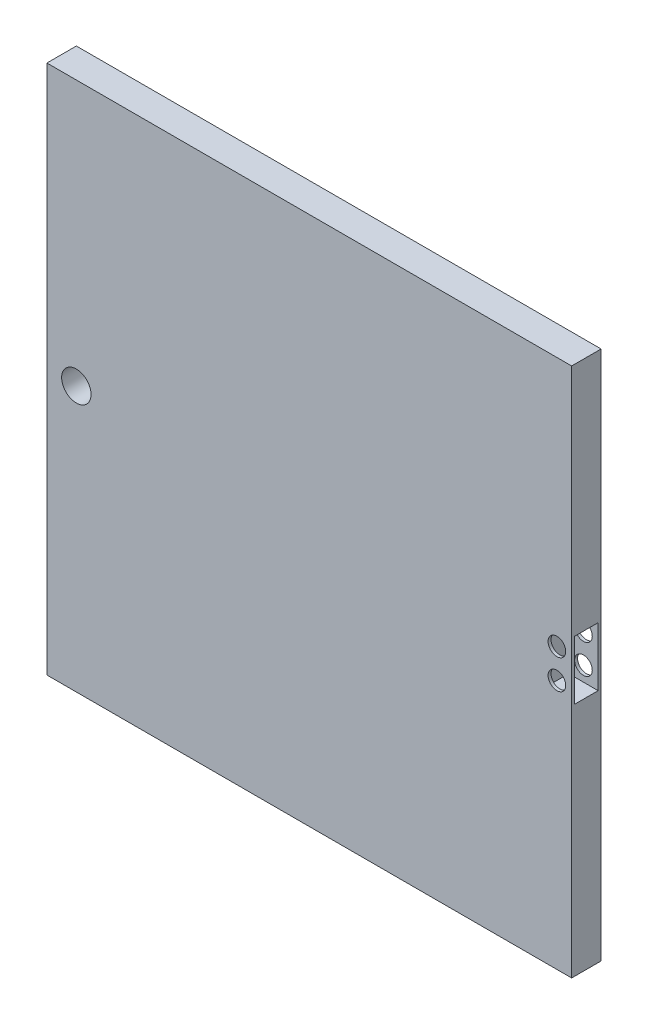
SolidWorks part; units mm, degrees
material "PET"
ref_plane "Front Plane" through (0, 0, 0) normal (0, 0, 1) x (1, 0, 0)
ref_plane "Top Plane" through (0, 0, 0) normal (0, 1, 0) x (1, 0, 0)
ref_plane "Right Plane" through (0, 0, 0) normal (1, 0, 0) x (0, 0, -1)
sketch "Sketch1" plane through (0, 0, 0) normal (0, 0, 1) x (1, 0, 0)
  line L1 (-78.2272, 89.1981) -> (148.0868, 89.1981)
  line L2 (-78.2272, 89.1981) -> (-78.2272, -126.7019)
  line L3 (-78.2272, -126.7019) -> (148.0868, -126.7019)
  line L4 (148.0868, 89.1981) -> (148.0868, -126.7019)
  dimension "D1" = 215.9
  dimension "D2" = 226.314
extrude "Boss-Extrude1" add sketch "Sketch1" along normal blind 12.7
sketch "Sketch2" plane through (148.0868, 0, 0) normal (1, 0, 0) x (0, 0, -1)
  line L1 (-11.43, 0.3061) -> (-1.27, 0.3061)
  line L2 (-11.43, 0.3061) -> (-11.43, -25.0939)
  line L3 (-11.43, -25.0939) -> (-1.27, -25.0939)
  line L4 (-1.27, 0.3061) -> (-1.27, -25.0939)
  line L6 (-12.7, -126.7019) -> (-12.7, 89.1981) construction
  point P6 (-6.35, 0.3061)
  point P8 (-1.27, -12.3939)
  dimension "D1" = 25.4
  dimension "D2" = 101.6
  dimension "D3" = 10.16
  dimension "D4" = 6.35
extrude "Cut-Extrude1" cut sketch "Sketch2" against normal blind 12.7
sketch "Sketch3" plane through (0, 0, 12.7) normal (0, 0, 1) x (1, 0, 0)
  line L0 (148.0868, 89.1981) -> (-78.2272, 89.1981) construction
  line L1 (-78.2272, 89.1981) -> (-78.2272, -126.7019) construction
  line L2 (148.0868, -126.7019) -> (148.0868, 89.1981) construction
  line L4 (135.3868, 0.3061) -> (148.0868, 0.3061) construction
  circle A0 centre (-65.5272, -12.4019) radius 6.35
  circle A1 centre (141.7368, -6.0439) radius 3.81
  circle A2 centre (141.7368, -18.7439) radius 3.81
  point P11 (0, 0)
  dimension "D1" = 101.6
  dimension "D3" = 6.35
  dimension "D5" = 7.62
  dimension "D7" = 12.7
  dimension "D2" = 12.7
  dimension "D4" = 6.35
  dimension "D6" = 2
extrude "Cut-Extrude2" cut sketch "Sketch3" against normal blind 12.7
sketch "Sketch4" plane through (0, 89.1981, 0) normal (0, 1, 0) x (1, 0, 0)
  line L1 (-78.2272, 0) -> (148.0868, 0)
  line L2 (-78.2272, 0) -> (-78.2272, -12.7)
  line L3 (-78.2272, -12.7) -> (148.0868, -12.7)
  line L4 (148.0868, 0) -> (148.0868, -12.7)
extrude "Boss-Extrude2" add sketch "Sketch4" along normal blind 12.7
